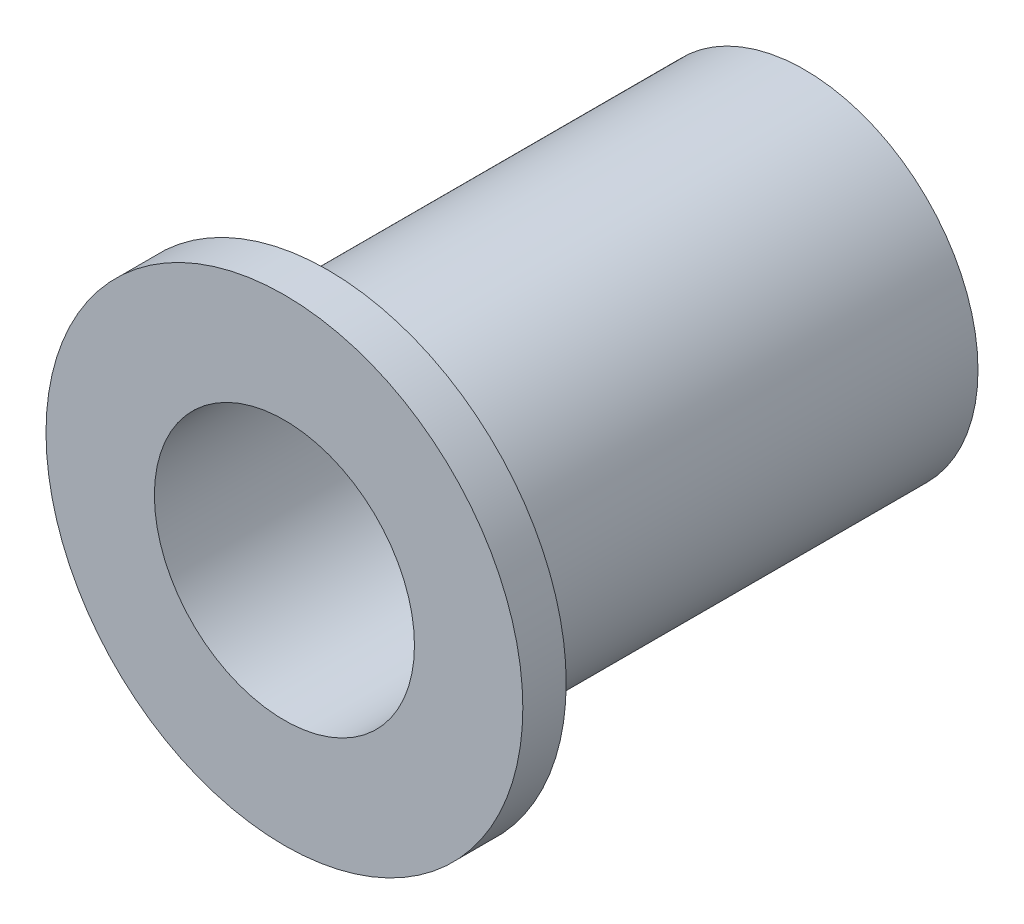
SolidWorks part; units mm, degrees
ref_plane "Front Plane" through (0, 0, 0) normal (0, 0, 1) x (1, 0, 0)
ref_plane "Top Plane" through (0, 0, 0) normal (0, 1, 0) x (1, 0, 0)
ref_plane "Right Plane" through (0, 0, 0) normal (1, 0, 0) x (0, 0, -1)
sketch "Sketch1" plane through (0, 0, 0) normal (0, 0, 1) x (1, 0, 0)
  circle A0 centre (0, 0) radius 4.7625
  circle A1 centre (0, 0) radius 6.35
extrude "Boss-Extrude1" add sketch "Sketch1" along normal blind 19.05
sketch "Sketch2" plane through (0, 0, 19.05) normal (0, 0, 1) x (1, 0, 0)
  circle A0 centre (0, 0) radius 8.7312
  circle A1 centre (0, 0) radius 4.7625
extrude "Boss-Extrude2" add sketch "Sketch2" against normal blind 1.5875
